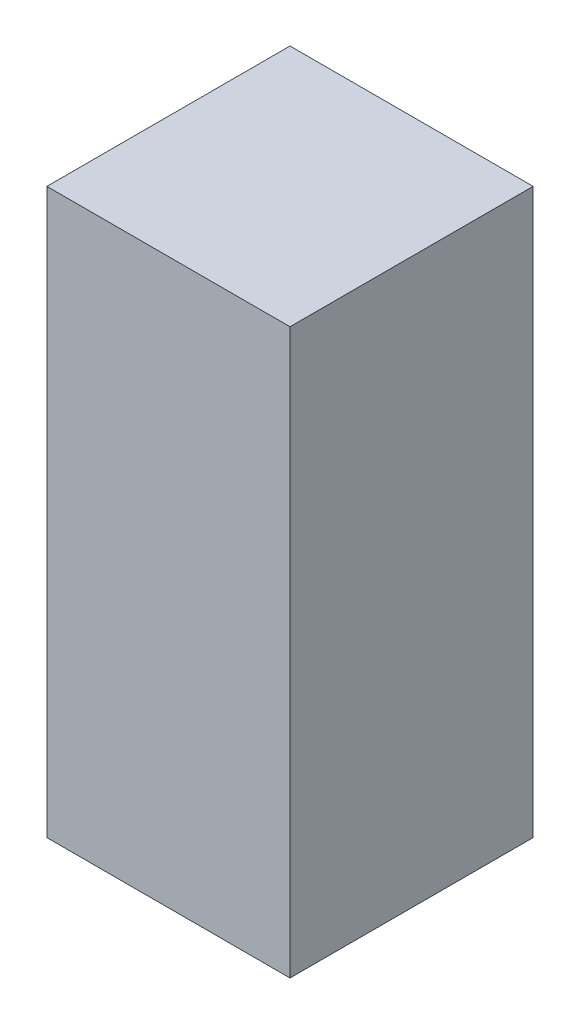
SolidWorks part; units mm, degrees
ref_plane "Front Plane" through (0, 0, 0) normal (0, 0, 1) x (1, 0, 0)
ref_plane "Top Plane" through (0, 0, 0) normal (0, 1, 0) x (1, 0, 0)
ref_plane "Right Plane" through (0, 0, 0) normal (1, 0, 0) x (0, 0, -1)
sketch "Sketch1" plane through (0, 0, 0) normal (0, 1, 0) x (1, 0, 0)
  line L1 (-12.7, -12.7) -> (12.7, -12.7)
  line L2 (-12.7, -12.7) -> (-12.7, 12.7)
  line L3 (-12.7, 12.7) -> (12.7, 12.7)
  line L4 (12.7, -12.7) -> (12.7, 12.7)
  line L5 (-12.7, -12.7) -> (12.7, 12.7) construction
  line L6 (-12.7, 12.7) -> (12.7, -12.7) construction
  point P0 (0, 0)
  dimension "D1" = 25.4
  dimension "D2" = 25.4
extrude "Boss-Extrude1" add sketch "Sketch1" along normal blind 58.928
